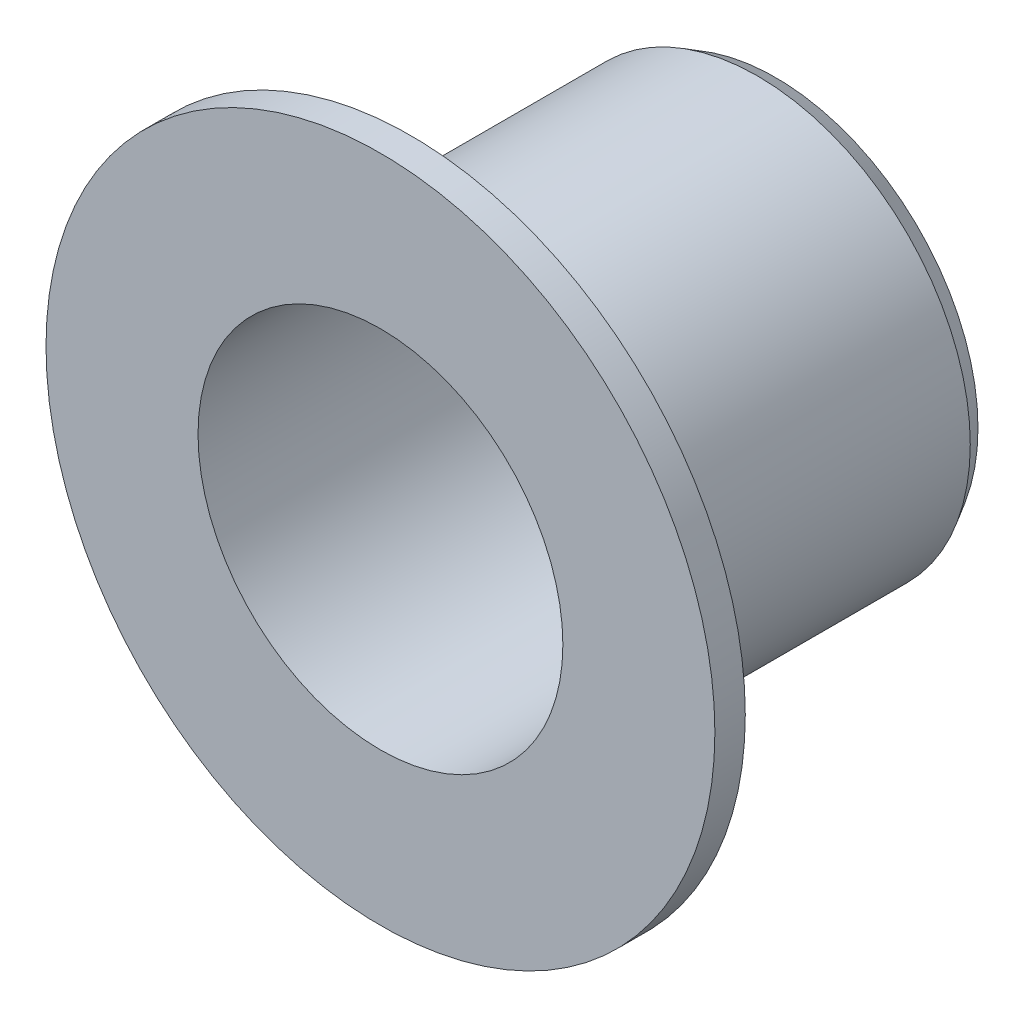
SolidWorks part; units mm, degrees
material "PTFE (geral)"
ref_plane "Front" through (0, 0, 0) normal (0, 0, 1) x (1, 0, 0)
ref_plane "Top" through (0, 0, 0) normal (0, 1, 0) x (1, 0, 0)
ref_plane "Right" through (0, 0, 0) normal (1, 0, 0) x (0, 0, -1)
sketch "Esboço1" plane through (0, 0, 0) normal (0, 0, 1) x (1, 0, 0)
  circle A0 centre (0, 0) radius 3.5
  circle A1 centre (0, 0) radius 3
  dimension "D1" = 6
  dimension "D2" = 7
extrude "Ressalto-extrusão1" add sketch "Esboço1" along normal blind 5.5
sketch "Esboço2" plane through (0, 0, 0) normal (0, 0, -1) x (-1, 0, 0)
  circle A0 centre (0, 0) radius 3.5
  circle A1 centre (0, 0) radius 3 construction
  circle A2 centre (0, 0) radius 3
extrude "Ressalto-extrusão2" add sketch "Esboço2" along normal blind 0.5
sketch "Esboço3" plane through (0, 0, 5.5) normal (0, 0, 1) x (1, 0, 0)
  circle A0 centre (0, 0) radius 5.5
  circle A1 centre (0, 0) radius 3 construction
  circle A2 centre (0, 0) radius 3
  dimension "D1" = 11
extrude "Ressalto-extrusão4" add sketch "Esboço3" along normal blind 0.5
fillet "Filete1" radius 0.5 1 edges at (3.5, 0, 5.5)
chamfer "Chanfro1" distance 0.3 angle 30 1 edges at (-3.5, 0, -0.5)
